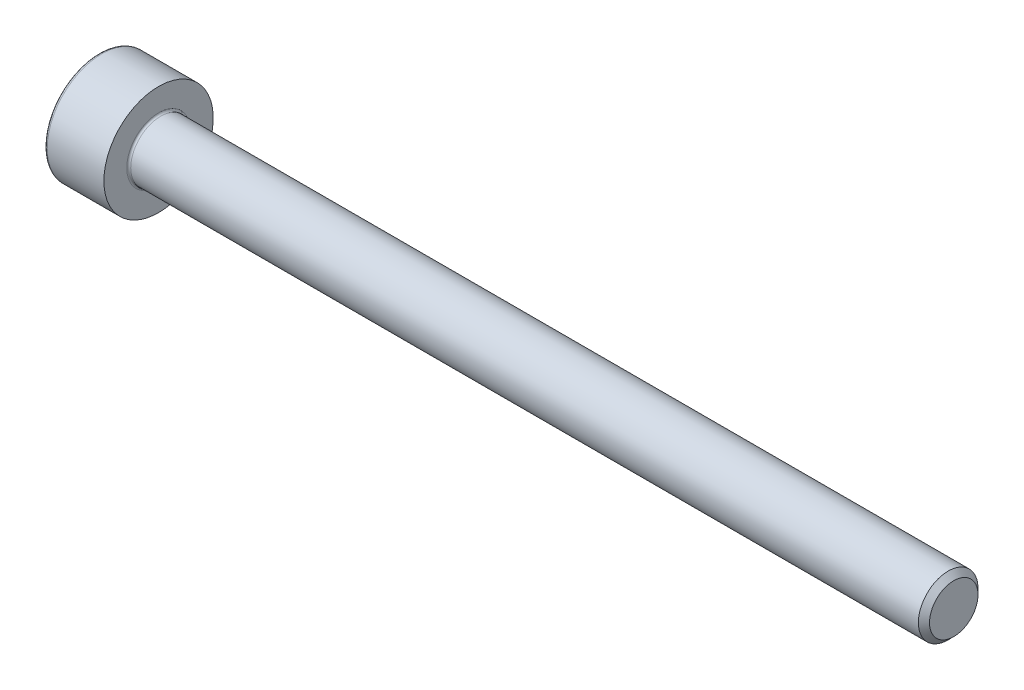
SolidWorks part; units mm, degrees
revolve "Base-Revolve" add sketch "BodySke"
sketch "BodySke" plane through (0, 0, 0) normal (0, 0, 1) x (1, 0, 0)
  line L0 (0, 0) -> (0, 2.75)
  line L1 (0, 2.75) -> (3, 2.75)
  line L2 (3, 2.75) -> (3, 1.5)
  line L3 (3, 1.5) -> (42.7195, 1.5)
  line L4 (43, 1.2195) -> (43, 0)
  line L5 (43, 0) -> (0, 0)
  line L6 (-31.75, 0) -> (127, 0) construction
  line L8 (43, 1.2195) -> (42.7195, 1.5)
  line L10 (43, -1.2195) -> (42.7195, -1.5) construction
  line L11 (3.5, 9.525) -> (3.5, 3.175) construction
  line L12 (38, 9.525) -> (38, 3.175) construction
  line L13 (-17, 9.525) -> (-17, 3.175) construction
  dimension "Head_ht" = 3
  dimension "Length" = 40
  dimension "Body_ch_ang" = 45
  dimension "Diameter" = 3
  dimension "Minor_dia" = 2.439
  dimension "Advance" = 0.5
  dimension "Thread_nom" = 5
  dimension "Thread_length" = 60
  dimension "Head_dia" = 5.5
cosmetic thread "ThreadCosmetic" [suppressed]
fillet "Fillet1" radius 0.1 1 edges at (3, 0, 1.5)
fillet "Fillet2" radius 0.15 1 edges at (0, 0, 2.75)
ref_plane "Plane1" through (0, 0, 0) normal (0, 0, 1) x (1, 0, 0)
ref_plane "Plane2" through (0, 0, 0) normal (0, 1, 0) x (1, 0, 0)
ref_plane "Plane3" through (0, 0, 0) normal (1, 0, 0) x (0, 0, -1)
sketch "Sketch2" plane through (0, 0, 0) normal (0, 0, 1) x (1, 0, 0)
  line L0 (0, 1.28) -> (1.3, 1.28)
  line L1 (1.3, 1.28) -> (2.039, 0)
  line L2 (-31.75, 0) -> (127, 0) construction
  line L3 (2.039, 0) -> (0, 0)
  line L4 (0, 0) -> (0, 1.28)
  line L6 (0, 0) -> (47.625, 0) construction
  dimension "D1" = 1.28
  dimension "D2" = 60
  dimension "Depth" = 1.3
revolve "Hex-PreBroach" cut sketch "Sketch2" angle 360 about L6
sketch "Sketch3" plane through (0, 0, 0) normal (-1, 0, 0) x (0, 0.5, 0.866)
  line L0 (0.739, 1.28) -> (-0.739, 1.28)
  line L1 (-0.739, 1.28) -> (-1.478, 0)
  line L2 (0.739, 1.28) -> (1.478, 0)
  line L3 (0.739, -1.28) -> (1.478, 0)
  line L4 (0.739, -1.28) -> (-0.739, -1.28)
  line L5 (-0.739, -1.28) -> (-1.478, 0)
  dimension "D1" = 1.28
  dimension "D2" = 1.28
  dimension "Hex_size" = 2.56
extrude "Hex" cut sketch "Sketch3" against normal blind 1.3
sketch "ThdSchSke" plane through (0, 0, 0) normal (0, 0, 1) x (1, 0, 0)
  line L0 (38, -1.2195) -> (37.8036, -1.5)
  line L1 (38, -1.2195) -> (38.1964, -1.5)
  line L2 (38.1964, -1.5) -> (38.1964, -1.875)
  line L3 (-3.175, 0) -> (5.1513, 0) construction
  line L4 (0, 2.6) -> (0, -2.6) construction
  line L5 (38.1964, -1.875) -> (37.8036, -1.875)
  line L6 (37.8036, -1.875) -> (37.8036, -1.5)
  dimension "Thread_minor" = 2.439
  dimension "Diameter" = 3
  dimension "Start" = 38
revolve "ThreadSchematic" [suppressed] cut sketch "ThdSchSke" angle 360 about L3
pattern_linear "ThdSchPat" [suppressed]
equation "\"D2@Sketch3\" = \"Hex_size@Sketch3\" / 2"
equation "\"D1@Sketch3\" = \"Hex_size@Sketch3\" / 2"
equation "\"D1@Sketch2\" = \"Hex_size@Sketch3\" / 2"
equation "\"Thread_minor@ThreadCosmetic\"  =  \"Minor_dia@BodySke\""
equation "\"Depth@Sketch2\" =  \"Key_eng@Hex\""
equation "\"Thread_length@ThreadCosmetic\" = ((sgn( (\"Length@BodySke\" - \"Advance@BodySke\" * 3.0) - \"Thread_nom@BodySke\" )-1)*( (\"Length@BodySke\" - \"Advance@BodySke\" * 3.0) - \"Thread_nom@BodySke\" ))/-2+ \"Thread_nom@BodySke\""
equation "\"Thread_minor@ThdSchSke\" = \"Minor_dia@BodySke\""
equation "\"Diameter@ThdSchSke\" = \"Diameter@BodySke\""
equation "\"Overcut@ThdSchSke\" = \"Diameter@BodySke\" * 1.25"
equation "\"Start@ThdSchSke\" = \"Head_ht@BodySke\" + \"Length@BodySke\" - \"Thread_length@ThreadCosmetic\"  '---Non-countersunk---"
equation "\"Num_threads@ThdSchPat\" = int( \"Thread_length@ThreadCosmetic\" / \"Advance@BodySke\" + 0.999 )  + 1"
equation "\"Advance@ThdSchPat\" = \"Thread_length@ThreadCosmetic\" /  (\"Num_threads@ThdSchPat\" - 1) 'relax it"
equation "\"Num_threads@ThdSchPat\" = \"Num_threads@ThdSchPat\" - sgn( \"Num_threads@ThdSchPat\" - 1) '---chamfered tips only---"
